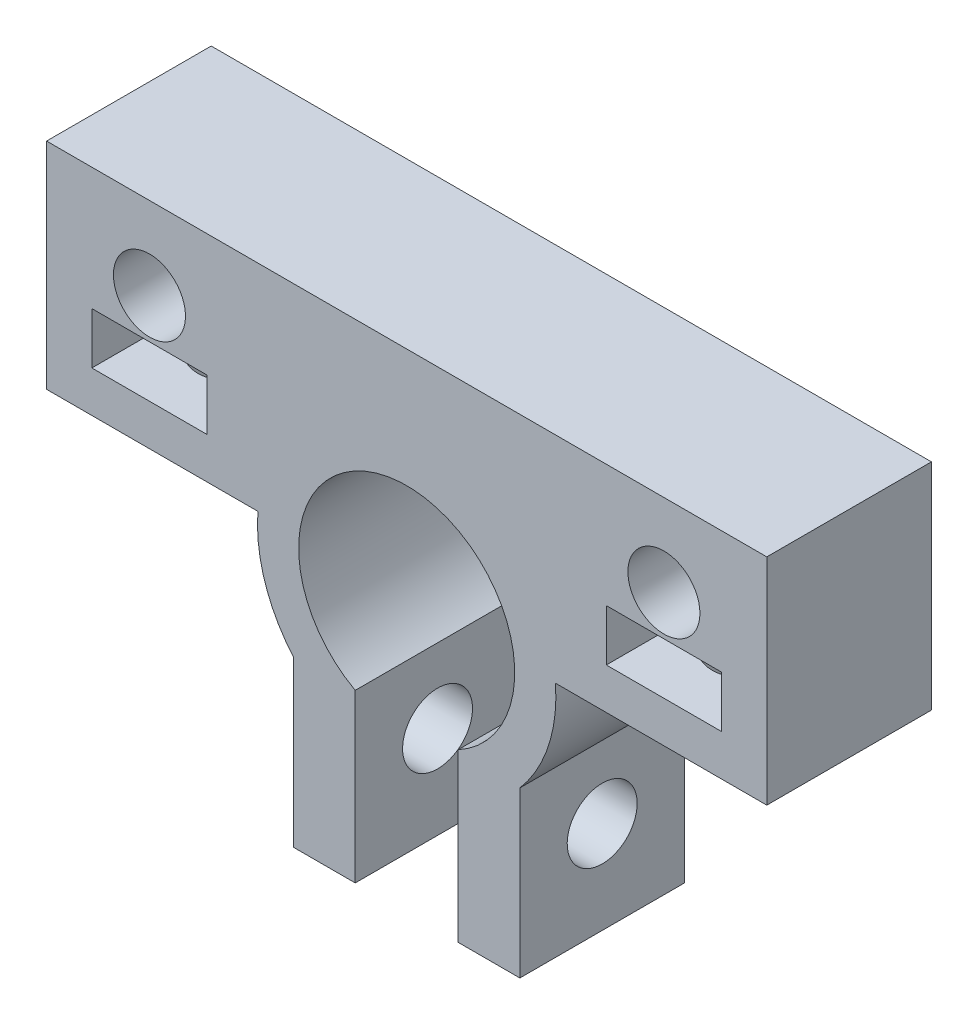
SolidWorks part; units mm, degrees
ref_plane "Plano frontal" through (0, 0, 0) normal (0, 0, 1) x (1, 0, 0)
ref_plane "Plano superior" through (0, 0, 0) normal (0, 1, 0) x (1, 0, 0)
ref_plane "Plano direito" through (0, 0, 0) normal (1, 0, 0) x (0, 0, -1)
sketch "Esboço1" plane through (0, 0, 0) normal (0, 0, 1) x (1, 0, 0)
  line L0 (17.5, 11) -> (0, 11)
  line L1 (15.3, 2.55) -> (9.7, 5.05) construction
  line L2 (0, 0) -> (0, 8.1134) construction
  line L3 (-17.5, 11) -> (0, 11)
  line L4 (-17.5, 0.55) -> (-7.2291, 0.55)
  line L5 (-5.5, -4.7236) -> (-5.5, -12.7236)
  line L6 (-5.5, -12.7236) -> (-2.5, -12.7236)
  line L7 (-2.5, -12.7236) -> (-2.5, -4.6165)
  line L8 (-17.5, 11) -> (-17.5, 0.55)
  line L9 (2.5, -12.7236) -> (2.5, -4.6165)
  line L10 (5.5, -12.7236) -> (2.5, -12.7236)
  line L11 (5.5, -4.7236) -> (5.5, -12.7236)
  line L12 (-15.3, 5.05) -> (-9.7, 5.05)
  line L13 (-15.3, 5.05) -> (-15.3, 2.55)
  line L14 (-15.3, 2.55) -> (-9.7, 2.55)
  line L15 (17.5, 11) -> (17.5, 0.55)
  line L16 (17.5, 0.55) -> (7.2291, 0.55)
  line L17 (-9.7, 5.05) -> (-9.7, 2.55)
  line L18 (-15.3, 5.05) -> (-9.7, 2.55) construction
  line L19 (-15.3, 2.55) -> (-9.7, 5.05) construction
  line L20 (15.3, 5.05) -> (9.7, 2.55) construction
  line L21 (9.7, 5.05) -> (9.7, 2.55)
  line L22 (15.3, 2.55) -> (9.7, 2.55)
  line L23 (15.3, 5.05) -> (15.3, 2.55)
  line L24 (15.3, 5.05) -> (9.7, 5.05)
  arc A1 (2.5, -4.6165) -> (-2.5, -4.6165) centre (0, 0) ccw
  arc A2 (7.2291, 0.55) -> (5.5, -4.7236) centre (0, 0) cw
  circle A3 centre (12.5, 7) radius 1.75
  circle A4 centre (-12.5, 7) radius 1.75
  arc A6 (-7.2291, 0.55) -> (-5.5, -4.7236) centre (0, 0) ccw
  point P1 (-17.5, 5.775)
  point P3 (-12.5, 3.8)
  point P19 (0, 0)
  point P29 (12.5, 3.8)
  point P30 (0, 10)
  dimension "D2" = 10.5
  dimension "D4" = 4
  dimension "D5" = 3.5
  dimension "D7" = 2
  dimension "D1" = 25
  dimension "D6" = 3
  dimension "D8" = 7
  dimension "D9" = 5
  dimension "D10" = 5
  dimension "D11" = 0.2
  dimension "D12" = 2.5
  dimension "D13" = 5.6
  dimension "D14" = 2
  dimension "D15" = 8
extrude "Ressalto-extrusão1" add sketch "Esboço1" along normal blind 8
sketch "Esboço2" plane through (0, 0.55, 0) normal (0, -1, 0) x (1, 0, 0)
  line L0 (0, 0) -> (0, 10.3612) construction
  line L1 (-15.3, 0) -> (-9.7, 0) construction
  line L2 (-15.3, 0) -> (-9.7, 0) construction
  line L3 (-17.5, 8) -> (-17.5, 0) construction
  circle A0 centre (-12.5, 4) radius 1.65
  circle A1 centre (12.5, 4) radius 1.65
  point P9 (-17.5, 4)
  point P10 (-12.5, 0)
  dimension "D1" = 3.3
extrude "Corte-extrusão1" cut sketch "Esboço2" against normal blind 7
sketch "Esboço3" plane through (-5.5, 0, 0) normal (-1, 0, 0) x (0, 0, 1)
  line L0 (8, -4.7236) -> (0, -4.7236) construction
  circle A0 centre (4, -8.2236) radius 1.7
  point P6 (4, -4.7236)
  dimension "D1" = 3.4
  dimension "D2" = 3.5
extrude "Corte-extrusão2" cut sketch "Esboço3" against normal through all
